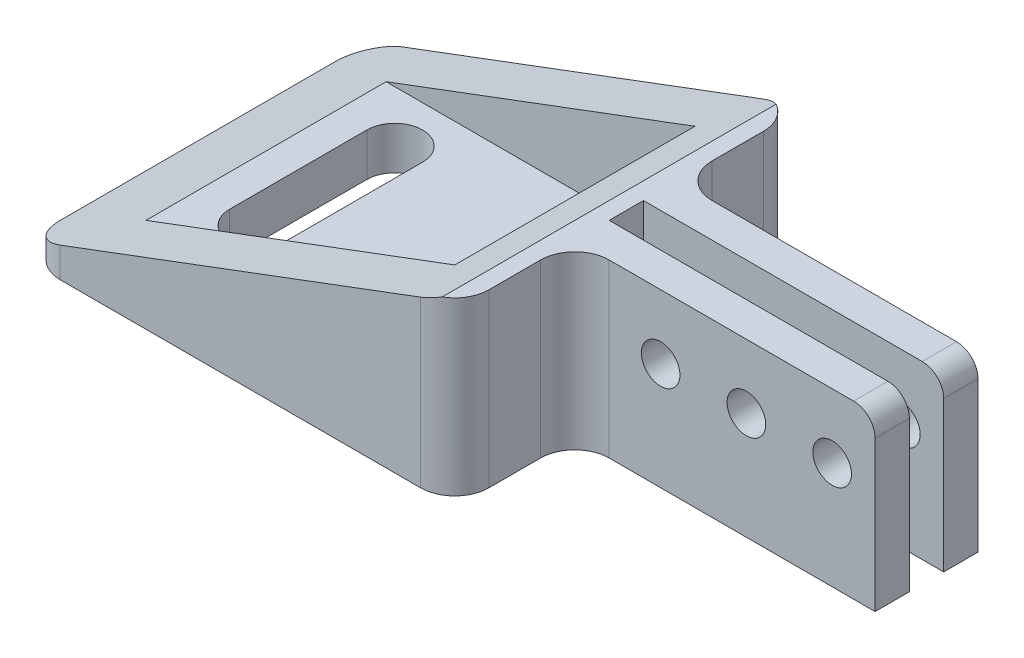
SolidWorks part; units mm, degrees
ref_plane "Front Plane" through (0, 0, 0) normal (0, 0, 1) x (1, 0, 0)
ref_plane "Top Plane" through (0, 0, 0) normal (0, 1, 0) x (1, 0, 0)
ref_plane "Right Plane" through (0, 0, 0) normal (1, 0, 0) x (0, 0, -1)
sketch "Sketch1" plane through (0, 0, 0) normal (0, 1, 0) x (1, 0, 0)
  line L1 (-25, -20) -> (25, -20)
  line L2 (-25, -20) -> (-25, 20)
  line L3 (-25, 20) -> (25, 20)
  line L4 (25, -20) -> (25, 20)
  line L5 (0, 20) -> (0, -20) construction
  line L6 (-25, 0) -> (25, 0) construction
  point P0 (0, 0)
  dimension "D1" = 40
  dimension "D2" = 50
extrude "Boss-Extrude1" add sketch "Sketch1" along normal blind 20
sketch "Sketch3" plane through (0, 20, 0) normal (0, 1, 0) x (1, 0, 0)
  line L0 (0, 0) -> (33.015, 0) construction
  line L1 (25, -2) -> (60, -2)
  line L2 (25, -20) -> (25, 20) construction
  line L3 (60, -2) -> (60, -6)
  line L4 (60, -6) -> (25, -6)
  line L5 (25, -6) -> (25, -2)
  dimension "D1" = 2
  dimension "D2" = 4
  dimension "D3" = 35
extrude "Boss-Extrude2" add sketch "Sketch3" along normal blind 20 from surface at -20 starting at face at (0, 0, 0)
sketch "Sketch4" plane through (0, 0, 6) normal (0, 0, 1) x (1, 0, 0)
  line L0 (60, 12.5) -> (25, 12.5) construction
  line L1 (60, 0) -> (60, 20) construction
  line L2 (25, 20) -> (25, 0) construction
  line L5 (60, 0) -> (25, 0) construction
  line L6 (60, 20) -> (60, 0) construction
  circle A0 centre (55, 12.5) radius 2.25
  dimension "D2" = 4.5
  dimension "D3" = 5
  dimension "D1" = 12.5
extrude "Cut-Extrude1" cut sketch "Sketch4" against normal blind 5
pattern_linear "LPattern1" count 3 spacing 10 along (-1, 0, 0) of "Cut-Extrude1"
mirror "Mirror1" about plane through (0, 0, 0) normal (0, 0, 1) of "LPattern1", "Cut-Extrude1", "Boss-Extrude2"
sketch "Sketch5" plane through (0, 0, 20) normal (0, 0, 1) x (1, 0, 0)
  line L0 (23, 20) -> (-25, 2)
  line L1 (-25, 2) -> (-25, 20)
  line L2 (-25, 20) -> (23, 20)
  line L3 (-25, 0) -> (25, 0) construction
  line L4 (-25, 20) -> (25, 20) construction
  line L5 (25, 20) -> (25, 0) construction
  dimension "D1" = 2
  dimension "D2" = 2
extrude "Cut-Extrude2" cut sketch "Sketch5" against normal through all both and the other way through all
sketch "Sketch6" plane through (0, 20, 0) normal (0, 1, 0) x (1, 0, 0)
  line L0 (-25, 20) -> (23, 20) construction
  line L1 (-19, -14) -> (19, -14)
  line L2 (-19, -14) -> (-19, 14)
  line L3 (-19, 14) -> (19, 14)
  line L4 (19, -14) -> (19, 14)
  line L5 (0, 14) -> (0, -14) construction
  line L6 (-19, 0) -> (19, 0) construction
  line L7 (-25, 20) -> (-25, -20) construction
  point P0 (0, 0)
  dimension "D1" = 6
  dimension "D2" = 6
extrude "Cut-Extrude3" cut sketch "Sketch6" against normal offset from surface (15 mm away) 5 up to face at (28.3333, 0, 0)
sketch "Sketch7" plane through (0, 5, 0) normal (0, 1, 0) x (1, 0, 0)
  line L0 (-25, 0) -> (25, 0) construction
  line L1 (-25, 20) -> (-25, -20) construction
  line L2 (25, -2) -> (25, 2) construction
  line L3 (10, 8) -> (10, -8) construction
  line L4 (13.25, 8) -> (13.25, -8)
  line L5 (6.75, 8) -> (6.75, -8)
  arc A0 (13.25, 8) -> (6.75, 8) centre (10, 8) ccw
  arc A1 (6.75, -8) -> (13.25, -8) centre (10, -8) ccw
  point P8 (10, 0)
  point P13 (0, 0)
  dimension "D1" = 6.5
  dimension "D2" = 10
  dimension "D3" = 16
extrude "Cut-Extrude4" cut sketch "Sketch7" against normal through all both and the other way through all
mirror "Mirror2" about plane through (0, 0, 0) normal (1, 0, 0) of "Cut-Extrude4"
fillet "Fillet1" radius 2.5 2 edges at (60, 20, -4) (60, 20, 4)
fillet "Fillet2" radius 4 2 edges at (25, 10, -6) (25, 10, 6)
fillet "Fillet3" radius 4 4 edges at (-25, 1, -20) (-25, 1, 20) (25, 10, -20) (25, 10, 20)
